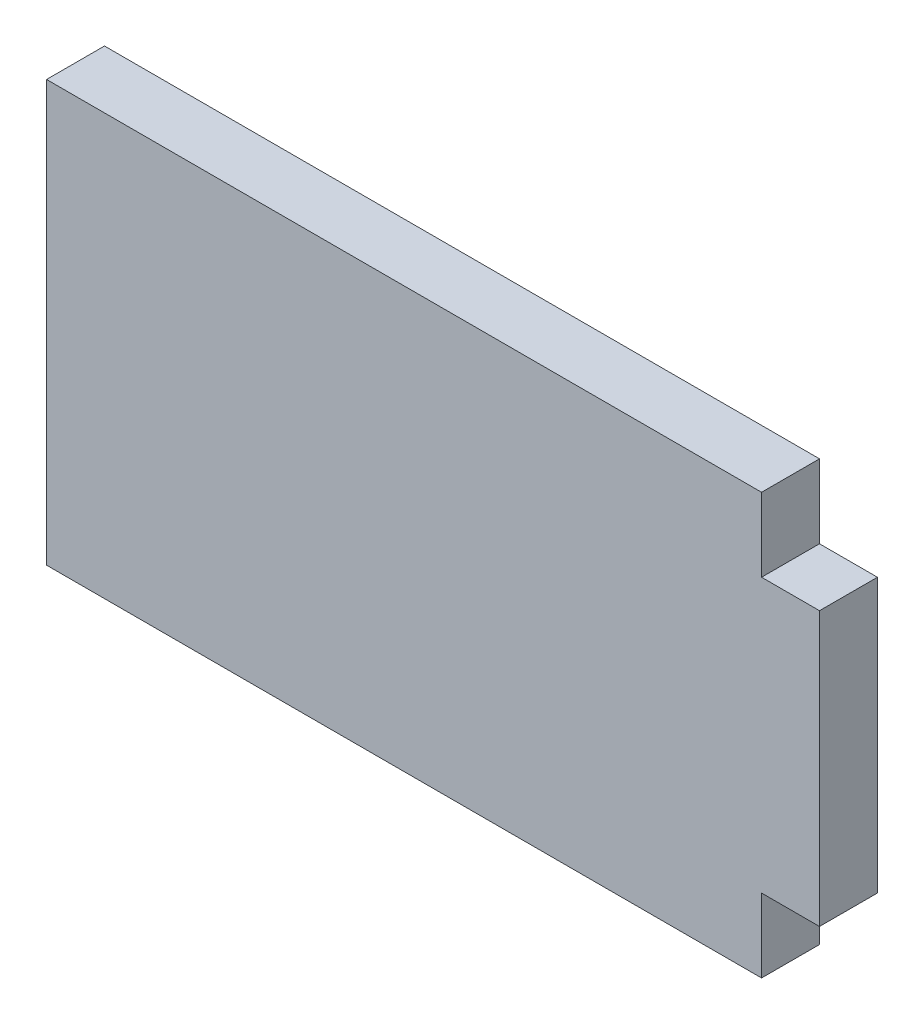
SolidWorks part; units mm, degrees
ref_plane "Front Plane" through (0, 0, 0) normal (0, 0, 1) x (1, 0, 0)
ref_plane "Top Plane" through (0, 0, 0) normal (0, 1, 0) x (1, 0, 0)
ref_plane "Right Plane" through (0, 0, 0) normal (1, 0, 0) x (0, 0, -1)
sketch "Sketch1" plane through (0, 0, 0) normal (0, 0, 1) x (1, 0, 0)
  line L9 (0, 21.78) -> (37.02, 21.78)
  line L10 (37.02, 21.78) -> (37.02, 17.97)
  line L11 (37.02, 17.97) -> (40.02, 17.97)
  line L12 (40.02, 17.97) -> (40.02, 3.81)
  line L13 (40.02, 3.81) -> (37.02, 3.81)
  line L14 (37.02, 3.81) -> (37.02, 0)
  line L15 (37.02, 0) -> (0, 0)
  line L16 (0, 0) -> (0, 21.78)
  point P0 (0, 10.89)
  point P1 (40.02, 10.89)
  dimension "D1" = 37.02
  dimension "D2" = 3.81
  dimension "D3" = 14.16
  dimension "D5" = 0
  dimension "D4" = 3
extrude "Boss-Extrude1" add sketch "Sketch1" along normal blind 3
